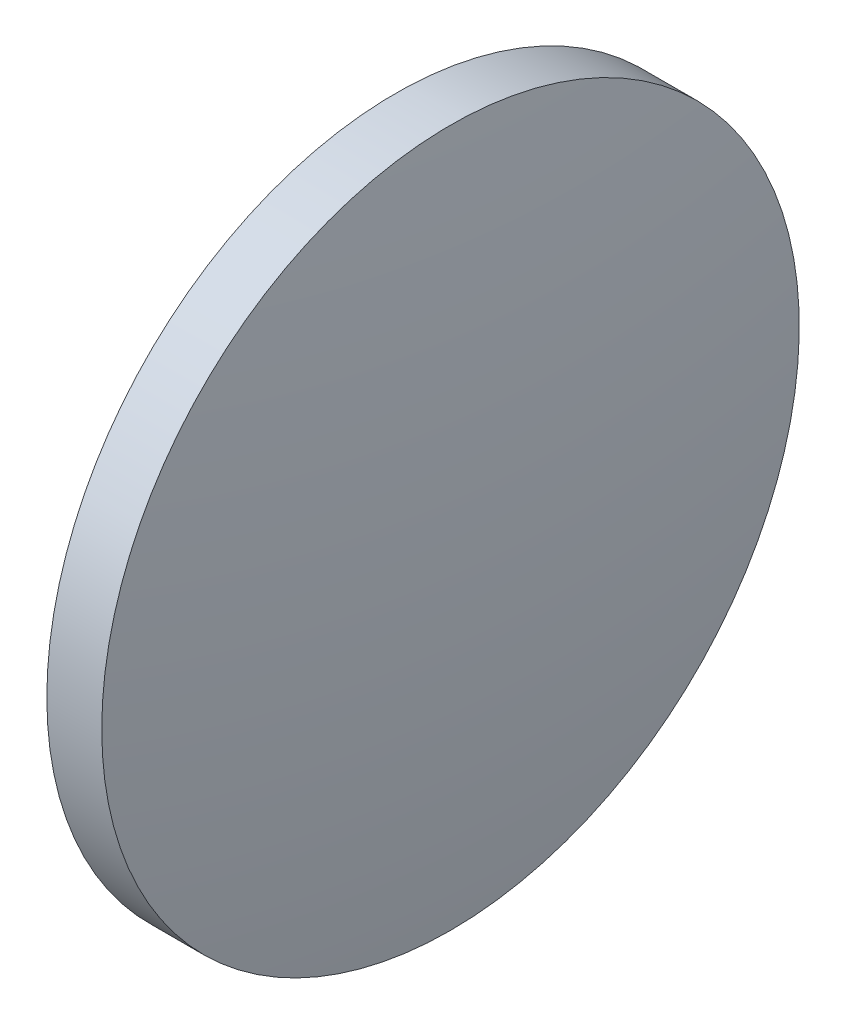
SolidWorks part; units mm, degrees
ref_plane "前视基准面" through (0, 0, 0) normal (0, 0, 1) x (1, 0, 0)
ref_plane "上视基准面" through (0, 0, 0) normal (0, 1, 0) x (1, 0, 0)
ref_plane "右视基准面" through (0, 0, 0) normal (1, 0, 0) x (0, 0, -1)
sketch "草图1" plane through (0, 0, 0) normal (0, 0, 1) x (1, 0, 0)
  line L0 (1071.6196, 150.681) -> (1090.4156, 150.681) construction
  line L1 (1077.3578, 150.681) -> (1077.3578, 163.381)
  line L2 (1077.3578, 163.381) -> (1079.3578, 163.381)
  line L3 (1080.2578, 150.681) -> (1077.3578, 150.681)
  arc A0 (1080.2578, 150.681) -> (1079.3578, 163.381) centre (990.2022, 150.681) ccw
revolve "旋转1" add sketch "草图1" angle 360 about L0
